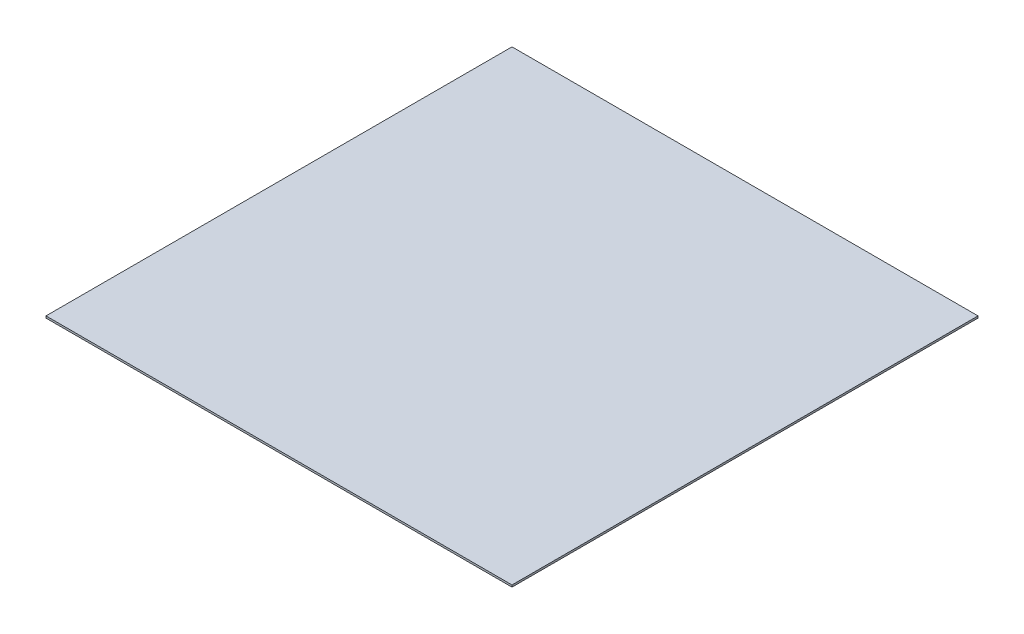
SolidWorks part; units mm, degrees
ref_plane "Front Plane" through (0, 0, 0) normal (0, 0, 1) x (1, 0, 0)
ref_plane "Top Plane" through (0, 0, 0) normal (0, 1, 0) x (1, 0, 0)
ref_plane "Right Plane" through (0, 0, 0) normal (1, 0, 0) x (0, 0, -1)
sketch "Sketch1" plane through (0, 0, 0) normal (0, 1, 0) x (1, 0, 0)
  line L1 (6000, -6000) -> (-6000, -6000)
  line L2 (6000, -6000) -> (6000, 6000)
  line L3 (6000, 6000) -> (-6000, 6000)
  line L4 (-6000, -6000) -> (-6000, 6000)
  line L5 (6000, -6000) -> (-6000, 6000) construction
  line L6 (6000, 6000) -> (-6000, -6000) construction
  point P0 (0, 0)
extrude "Boss-Extrude1" add sketch "Sketch1" along normal blind 50
